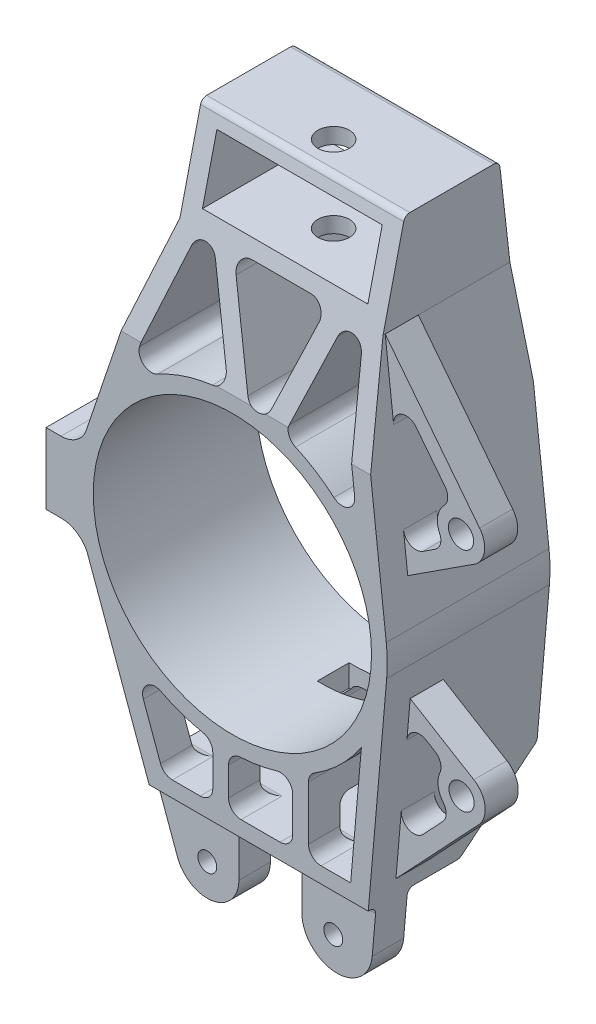
SolidWorks part; units mm, degrees
ref_plane "Front Plane" through (0, 0, 0) normal (0, 0, 1) x (1, 0, 0)
ref_plane "Top Plane" through (0, 0, 0) normal (0, 1, 0) x (1, 0, 0)
ref_plane "Right Plane" through (0, 0, 0) normal (1, 0, 0) x (0, 0, -1)
sketch "Sketch1" plane through (0, 0, 0) normal (0, 0, 1) x (1, 0, 0)
  line L0 (-24.3331, 81.8767) -> (-46.6088, 15.6856)
  line L1 (-24.3331, 111.3767) -> (40.1669, 111.3767)
  line L2 (-24.3331, 111.3767) -> (-24.3331, 81.8767)
  line L4 (40.1669, 111.3767) -> (40.1669, 81.8767)
  line L5 (40.1669, 81.8767) -> (48.8613, 5.567)
  line L7 (-1.4898, 81.8767) -> (17.3237, 81.8767)
  line L8 (-18.3331, 106.3767) -> (34.1669, 106.3767)
  line L9 (-18.3331, 106.3767) -> (-18.3331, 86.8767)
  line L10 (-18.3331, 86.8767) -> (34.1669, 86.8767)
  line L11 (34.1669, 106.3767) -> (34.1669, 86.8767)
  line L20 (-24.3331, 81.8767) -> (40.1669, 81.8767) construction
  line L23 (-94.694, 0) -> (182.7969, 0) construction
  line L24 (41.8901, -85.4419) -> (48.9903, -4.2861)
  line L25 (-19.916, -89.0664) -> (-46.2117, -16.8197)
  line L26 (0, -49.1774) -> (0, -71.1774) construction
  line L27 (-26.4271, -71.1774) -> (43.1381, -71.1774) construction
  line L28 (-17.5098, -95.6774) -> (40.9946, -95.6774) construction
  line L29 (-5.2265, 76.4496) -> (4.4727, 51.0532)
  line L30 (11.9744, 51.1292) -> (21.0886, 76.5256)
  line L31 (34.9275, 74.8611) -> (38.8293, 40.6146)
  line L32 (27.1883, 75.7594) -> (17.9116, 49.9101)
  line L33 (-12.0228, 77.4277) -> (-3.136, 54.1586)
  line L34 (-19.5506, 77.2764) -> (-29.4531, 47.8516)
  line L35 (-0.4271, -71.1774) -> (19.5729, -71.1774)
  line L36 (-28.2752, -48.5569) -> (-22.8198, -63.5455)
  line L37 (-19.061, -66.1774) -> (-10.2277, -66.1774)
  line L38 (-6.2277, -62.1774) -> (-6.2277, -52.1846)
  line L39 (24.1566, -45.1115) -> (24.1566, -62.1774)
  line L40 (28.1566, -66.1774) -> (37.5526, -66.1774)
  line L41 (37.5526, -66.1774) -> (40.9615, -27.2135)
  line L42 (-1.2277, -53.1051) -> (-1.2277, -62.1774)
  line L43 (2.7723, -66.1774) -> (15.1566, -66.1774)
  line L44 (19.1566, -62.1774) -> (19.1566, -50.9717)
  line L45 (-26.4271, -71.1774) -> (43.1381, -71.1774) construction
  line L46 (-0.4271, -71.1774) -> (-0.4271, -85.6774)
  line L47 (19.5729, -71.1774) -> (19.5729, -85.6774)
  line L48 (-10.4745, -85.6299) -> (55.2781, -85.6299) construction
  line L49 (0, 0) -> (0, -266.4589) construction
  line L50 (0, -266.4589) -> (0, 244.2731) construction
  arc A3 (-46.6088, 15.6856) -> (-46.2117, -16.8197) centre (0, 0) ccw
  arc A6 (-32.5224, -36.8879) -> (-6.2277, -48.7815) centre (0, 0) ccw construction
  arc A7 (34.9275, 74.8611) -> (27.1883, 75.7594) centre (30.9532, 74.4083) ccw
  arc A8 (-12.0228, 77.4277) -> (-19.5506, 77.2764) centre (-15.7595, 76.0005) ccw
  arc A9 (4.4727, 51.0532) -> (11.9744, 51.1292) centre (8.2095, 52.4803) ccw
  arc A10 (17.3237, 81.8767) -> (21.0886, 76.5256) centre (17.3237, 77.8767) cw
  arc A11 (-1.4898, 81.8767) -> (-5.2265, 76.4496) centre (-1.4898, 77.8767) ccw
  arc A12 (-23.7318, 43.0723) -> (-6.3557, 48.765) centre (0, 0) cw
  arc A13 (20.046, 44.9064) -> (32.2333, 37.1408) centre (0, 0) cw
  arc A14 (38.8293, 40.6146) -> (32.2333, 37.1408) centre (34.8551, 40.1617) cw
  arc A15 (17.9116, 49.9101) -> (20.046, 44.9064) centre (21.6765, 48.559) ccw
  arc A16 (-3.136, 54.1586) -> (-6.3557, 48.765) centre (-6.8727, 52.7315) cw
  arc A17 (-29.4531, 47.8516) -> (-23.7318, 43.0723) centre (-25.662, 46.5757) ccw
  arc A18 (-22.6723, -43.6393) -> (-9.4584, -48.2593) centre (0, 0) ccw
  arc A19 (-1.2277, -49.1621) -> (19.1566, -45.2929) centre (0, 0) ccw construction
  arc A20 (2.5637, -49.1106) -> (14.0165, -47.1376) centre (0, 0) ccw
  arc A21 (24.1566, -42.8355) -> (40.9615, -27.2135) centre (0, 0) ccw construction
  arc A22 (26.0387, -41.7182) -> (40.9615, -27.2135) centre (0, 0) ccw
  arc A23 (48.9903, -4.2861) -> (-46.2117, -16.8197) centre (0, 0) ccw construction
  arc A24 (48.9903, -4.2861) -> (48.8613, 5.567) centre (0, 0) ccw
  arc A25 (-1.2277, -62.1774) -> (2.7723, -66.1774) centre (2.7723, -62.1774) ccw
  arc A26 (15.1566, -66.1774) -> (19.1566, -62.1774) centre (15.1566, -62.1774) ccw
  arc A27 (19.1566, -50.9717) -> (14.0165, -47.1376) centre (15.1566, -50.9717) ccw
  arc A28 (-1.2277, -53.1051) -> (2.5637, -49.1106) centre (2.7723, -53.1051) cw
  arc A29 (-6.2277, -52.1846) -> (-9.4584, -48.2593) centre (-10.2277, -52.1846) ccw
  arc A30 (-10.2277, -66.1774) -> (-6.2277, -62.1774) centre (-10.2277, -62.1774) ccw
  arc A31 (-22.8198, -63.5455) -> (-19.061, -66.1774) centre (-19.061, -62.1774) ccw
  arc A32 (-28.2752, -48.5569) -> (-22.6723, -43.6393) centre (-24.5164, -47.1888) cw
  arc A33 (24.1566, -62.1774) -> (28.1566, -66.1774) centre (28.1566, -62.1774) ccw
  arc A34 (24.1566, -45.1115) -> (26.0387, -41.7182) centre (28.1566, -45.1115) cw
  arc A35 (-0.4271, -85.6774) -> (-19.916, -89.0664) centre (-10.4745, -85.6299) cw
  arc A36 (19.5729, -85.6774) -> (41.8901, -85.4419) centre (30.72, -84.4646) ccw
  circle A37 centre (-10.4745, -85.6299) radius 3
  circle A38 centre (29.5255, -85.6299) radius 3
  circle A39 centre (0, 0) radius 44.1774
  point P1 (24.1566, -53.6445)
  point P46 (40.2351, 28.2765)
  point P49 (16.6113, 46.287)
  point P52 (-1.2277, 49.1621)
  point P55 (-33.4139, 36.0823)
  point P65 (7.9169, 81.8767)
  point P66 (7.9169, 106.3767)
  point P85 (8.25, 48.4805)
  point P100 (-0.4271, -71.1774)
  point P101 (19.5729, -71.1774)
  dimension "D14" = 98.3549
  dimension "D12" = 98.3549
  dimension "D13" = 24.5
  dimension "D15" = 4
  dimension "D16" = 4
  dimension "D28" = 4
  dimension "D29" = 4
  dimension "D32" = 69.5652
  dimension "D33" = 26
  dimension "D35" = 6
  dimension "D36" = 40
  dimension "D37" = 5
  dimension "D2" = 64.5
  dimension "D3" = 96.5
  dimension "D4" = 29.5
  dimension "D5" = 108.6
  dimension "D6" = 5
  dimension "D7" = 5
  dimension "D8" = 6
  dimension "D9" = 6
  dimension "D10" = 85
  dimension "D11" = 70
  dimension "D17" = 22
  dimension "D18" = 6
  dimension "D19" = 6
  dimension "D20" = 6
  dimension "D21" = 6
  dimension "D22" = 4.4727
  dimension "D23" = 5
  dimension "D24" = 6
  dimension "D25" = 6
  dimension "D26" = 5
  dimension "D27" = 5
  dimension "D30" = 19.1566
  dimension "D31" = 10
  dimension "D34" = 20
extrude "Boss-Extrude1" add sketch "Sketch1" along normal mid plane 51.67
sketch "Sketch3" plane through (0, 0, 0) normal (1, 0, 0) x (0, 0, -1)
  line L0 (25.835, -95.6774) -> (25.835, -71.1774)
  line L2 (25.835, -71.1774) -> (25.335, -71.1774)
  line L3 (23.335, -73.1774) -> (23.335, -95.6774)
  line L4 (-25.835, -95.6774) -> (25.835, -95.6774) construction
  line L5 (23.335, -95.6774) -> (25.835, -95.6774)
  line L6 (13.335, -95.6774) -> (13.335, -73.1774)
  line L7 (11.335, -71.1774) -> (-2.3541, -71.1774)
  line L8 (-3.7469, -70.6127) -> (-25.835, -49.1774)
  line L9 (-25.835, 49.1774) -> (-18.9504, 109.6031)
  line L10 (-25.835, 5.567) -> (-25.835, 81.8767) construction
  line L11 (0, 49.1774) -> (0, -16.8197) construction
  line L12 (0, 49.1774) -> (0, -16.8197)
  line L13 (-3.165, -71.1774) -> (-3.165, -49.1774) construction
  line L14 (-25.835, -85.4419) -> (-25.835, -4.2861) construction
  line L15 (-25.835, -49.1774) -> (-25.835, -95.6774)
  line L16 (-25.835, -95.6774) -> (13.335, -95.6774)
  line L17 (-25.835, 111.3767) -> (25.835, 111.3767) construction
  line L19 (11.6136, 109.8333) -> (25.835, 49.1774)
  line L20 (25.835, 5.567) -> (25.835, 81.8767) construction
  line L21 (-25.835, 49.1774) -> (55.9748, 49.1774) construction
  line L22 (55.9748, 49.1774) -> (-136.4579, 49.1774) construction
  line L23 (-25.835, 49.1774) -> (-25.835, 111.3767)
  line L24 (-25.835, 111.3767) -> (-16.9632, 111.3767)
  line L25 (9.6664, 111.3767) -> (25.835, 111.3767)
  line L26 (25.835, 111.3767) -> (25.835, 49.1774)
  arc A0 (25.335, -71.1774) -> (23.335, -73.1774) centre (25.335, -73.1774) ccw
  arc A1 (-18.9504, 109.6031) -> (-16.9632, 111.3767) centre (-16.9632, 109.3767) cw
  arc A2 (9.6664, 111.3767) -> (11.6136, 109.8333) centre (9.6664, 109.3767) cw
  arc A3 (13.335, -73.1774) -> (11.335, -71.1774) centre (11.335, -73.1774) ccw
  arc A4 (-2.3541, -71.1774) -> (-3.7469, -70.6127) centre (-2.3541, -69.1774) cw
  point P11 (13.335, -95.6774)
  point P30 (-20.3336, 111.3767)
  point P49 (13.335, -71.1774)
  dimension "D2" = 2
  dimension "D10" = 2
  dimension "D11" = 2
  dimension "D15" = 2
  dimension "D16" = 2
  dimension "D1" = 24.5
  dimension "D3" = 2.5
  dimension "D4" = 71.1774
  dimension "D5" = 10
  dimension "D6" = 16.5
  dimension "D7" = 22
  dimension "D8" = 6.5
  dimension "D9" = 30
  dimension "D12" = 11.6136
  dimension "D13" = 109.8333
  dimension "D14" = 9.6664
extrude "Cut-Extrude1" cut sketch "Sketch3" against normal through all both and the other way through all contours L15 L16 L6 L7 L8 | L9 A1 L24 L23 | L19 L26 L25 A2 | L0 L2 A0 L3 L5
fillet "Fillet1" radius 2 4 edges at (-31.2419, -49.1774, 25.835) (-2.7875, -49.1774, 25.835) (21.4441, -49.1774, 25.835) (42.0514, -49.1774, 25.835)
ref_plane "Plane1" through (0, 0, -6.985) normal (0, 0, 1) x (1, 0, 0)
sketch "Sketch5" plane through (0, 0, -6.985) normal (0, 0, 1) x (1, 0, 0)
  line L0 (40.1669, 81.8767) -> (70.1477, 43.5031)
  line L2 (48.8613, 5.567) -> (43.8925, 49.1774) construction
  line L3 (40.1669, 81.8767) -> (-107.5108, 81.8767) construction
  line L4 (47.3282, 19.0234) -> (69.0309, 33.1173)
  line L5 (49.9821, 61.1925) -> (59.188, 49.4095)
  line L6 (52.1168, 28.095) -> (56.0146, 30.6262)
  line L8 (42.8558, 58.2771) -> (40.1669, 81.8767)
  line L9 (47.3282, 19.0234) -> (45.964, 30.9968)
  line L10 (64.2376, 38.8857) -> (64.2376, -92.1903) construction
  line L11 (48.1076, -14.3753) -> (68.3061, -26.608)
  line L12 (45.1368, -48.3314) -> (48.9903, -4.2861) construction
  line L13 (43.5755, -66.1774) -> (69.8882, -38.1573)
  line L14 (45.0113, -49.7667) -> (43.1875, -70.6127) construction
  line L16 (8.9644, -66.1774) -> (144.1384, -66.1774) construction
  line L17 (15.1566, -66.1774) -> (2.7723, -66.1774) construction
  line L19 (53.1187, -23.2556) -> (55.9633, -24.9784)
  line L20 (52.1876, -49.7024) -> (58.4383, -43.0461)
  line L22 (47.0619, -26.3285) -> (48.1076, -14.3753)
  line L23 (45.287, -46.6156) -> (43.5755, -66.1774)
  arc A0 (70.1477, 43.5031) -> (69.0309, 33.1173) centre (64.2376, 38.8857) cw
  circle A1 centre (64.2376, 38.8857) radius 4
  circle A2 centre (64.2376, 38.8857) radius 7.5 construction
  arc A3 (58.8887, 44.143) -> (57.454, 35.6869) centre (64.2376, 38.8857) ccw
  arc A4 (49.9821, 61.1925) -> (42.8558, 58.2771) centre (46.8301, 58.7299) ccw
  arc A5 (52.1168, 28.095) -> (45.964, 30.9968) centre (49.9383, 31.4496) cw
  arc A6 (56.0146, 30.6262) -> (57.454, 35.6869) centre (53.836, 33.9809) ccw
  arc A7 (59.188, 49.4095) -> (58.8887, 44.143) centre (56.036, 46.9469) cw
  arc A8 (69.8882, -38.1573) -> (68.3061, -26.608) centre (64.4209, -33.0232) ccw
  circle A9 centre (64.4209, -33.0232) radius 4
  circle A10 centre (64.4209, -33.0232) radius 7.5 construction
  arc A11 (57.5537, -30.008) -> (58.6176, -37.7741) centre (64.4209, -33.0232) ccw
  arc A12 (52.1876, -49.7024) -> (45.287, -46.6156) centre (49.2717, -46.9642) cw
  arc A13 (58.4383, -43.0461) -> (58.6176, -37.7741) centre (55.5224, -40.3079) ccw
  arc A14 (55.9633, -24.9784) -> (57.5537, -30.008) centre (53.8912, -28.3998) cw
  arc A15 (53.1187, -23.2556) -> (47.0619, -26.3285) centre (51.0466, -26.6771) ccw
  point P25 (59.6257, 32.9713)
  point P28 (61.8542, 45.9969)
  point P53 (61.4029, -39.8892)
  point P56 (59.6676, -27.2218)
  dimension "D3" = 7.5
  dimension "D5" = 8
  dimension "D9" = 4
  dimension "D13" = 7.5
  dimension "D14" = 8
  dimension "D17" = 4
  dimension "D1" = 63.26
  dimension "D2" = 128
  dimension "D4" = 33
  dimension "D6" = 64.2376
  dimension "D7" = 5
  dimension "D8" = 5
  dimension "D10" = 133.2
  dimension "D11" = 52
  dimension "D12" = 31.2
  dimension "D15" = 5
  dimension "D16" = 5
extrude "Boss-Extrude2" add sketch "Sketch5" against normal blind 10.5
ref_plane "Plane2" through (0, 0, 0.535) normal (0, 0, 1) x (1, 0, 0)
sketch "Sketch6" plane through (0, 0, 0.535) normal (0, 0, 1) x (1, 0, 0)
  line L1 (-59.1738, 10.6856) -> (-59.1738, -11.8197)
  line L3 (-46.2117, -16.8197) -> (-221.7948, -16.8197) construction
  line L4 (-46.6088, 15.6856) -> (-235.4497, 15.6856) construction
  line L5 (-59.1738, 10.6856) -> (-54.4122, 10.6856)
  line L6 (-59.1738, -11.8197) -> (-54.4122, -11.8197)
  arc A0 (-46.6088, 15.6856) -> (-46.2117, -16.8197) centre (0, 0) ccw construction
  arc A1 (-46.6088, 15.6856) -> (-46.2117, -16.8197) centre (0, 0) ccw
  arc A2 (-54.4122, -11.8197) -> (-46.2117, -16.8197) centre (-54.4122, -21.0445) cw
  arc A3 (-54.4122, 10.6856) -> (-46.6088, 15.6856) centre (-54.4122, 19.2749) ccw
  point P11 (-49.1738, -0.6008)
  dimension "D1" = 5
  dimension "D4" = 9.2249
  dimension "D2" = 5
  dimension "D3" = 10
extrude "Boss-Extrude3" add sketch "Sketch6" against normal up to surface (26.37 mm away) up to face at (30.0885, -51.6598, -25.835)
sketch "Sketch7" plane through (-59.1738, 0, 0) normal (-1, 0, 0) x (0, 0, 1)
  line L0 (-25.835, -0.567) -> (0, 0) construction
  line L1 (-25.835, -11.8197) -> (-25.835, 10.6856) construction
  line L3 (-6.985, -168.7917) -> (-6.985, 168.7917) construction
  circle A0 centre (-16.9826, -0.3727) radius 2.75
  circle A1 centre (-6.985, -0.1533) radius 2.75
  dimension "D1" = 5.5
  dimension "D2" = 10
extrude "Cut-Extrude2" cut sketch "Sketch7" against normal up to surface (9.9977 mm away)
sketch "Sketch10" plane through (0, 111.3767, 0) normal (0, 1, 0) x (1, 0, 0)
  line L0 (40.1669, 9.6664) -> (-24.3331, 9.6664) construction
  line L1 (-24.3331, 11.6136) -> (40.1669, 11.6136) construction
  circle A0 centre (7.9169, 1.6136) radius 5
  point P5 (7.9169, 9.6664)
  dimension "D1" = 10
  dimension "D2" = 10
extrude "Cut-Extrude4" cut sketch "Sketch10" against normal up to surface (29.5 mm away) up to face at (7.9169, 81.8767, 1.9705)
sketch "Sketch11" plane through (0, 0, 0) normal (1, 0, 0) x (0, 0, -1)
  line L0 (12.835, -66.1774) -> (0.0786, -66.1774)
  line L1 (-2.0106, -65.3303) -> (-8.8552, -58.6881)
  line L2 (-6.7659, -53.5352) -> (12.835, -53.5352)
  line L3 (15.835, -56.5352) -> (15.835, -63.1774)
  line L4 (11.335, -71.1774) -> (-2.3541, -71.1774) construction
  line L6 (-3.7469, -70.6127) -> (-25.2278, -49.7667) construction
  line L7 (25.835, -16.8197) -> (25.835, -71.1774) construction
  arc A0 (-8.8552, -58.6881) -> (-6.7659, -53.5352) centre (-6.7659, -56.5352) cw
  arc A1 (0.0786, -66.1774) -> (-2.0106, -65.3303) centre (0.0786, -63.1774) cw
  arc A2 (12.835, -66.1774) -> (15.835, -63.1774) centre (12.835, -63.1774) ccw
  arc A3 (12.835, -53.5352) -> (15.835, -56.5352) centre (12.835, -56.5352) cw
  point P6 (4.4905, -71.1774)
  point P14 (-14.165, -53.5352)
  point P21 (15.835, -53.5352)
  dimension "D5" = 3
  dimension "D1" = 5
  dimension "D2" = 5
  dimension "D3" = 10
  dimension "D4" = 30
extrude "Cut-Extrude5" cut sketch "Sketch11" against normal through all and the other way up to vertex
sketch "Sketch12" plane through (0, 0, 0) normal (0, 1, 0) x (1, 0, 0)
  line L0 (-1.2277, -12.4391) -> (-1.2277, -2.3541)
  line L1 (-26.4271, -2.3541) -> (43.1381, -2.3541) construction
  line L2 (-1.2277, -21.7877) -> (-1.2277, 25.835) construction
  line L3 (-1.2277, -2.3541) -> (19.1566, -2.3541)
  line L4 (19.1566, -2.3541) -> (19.1566, -12.4391)
  line L5 (19.1566, -23.9861) -> (19.1566, 25.835) construction
  line L6 (-1.2277, -12.4391) -> (19.1566, -12.4391)
extrude "Cut-Extrude6" cut sketch "Sketch12" against normal offset from surface (51.1774 mm away) 20 up to face at (8.7613, -71.1774, -16.1368)
mirror "Mirror1" about plane through (0, 0, 0) normal (0, 0, 1) of bodies 109
delete or keep bodies "Body-Delete/Keep 1" type keep bodies bodies 110
